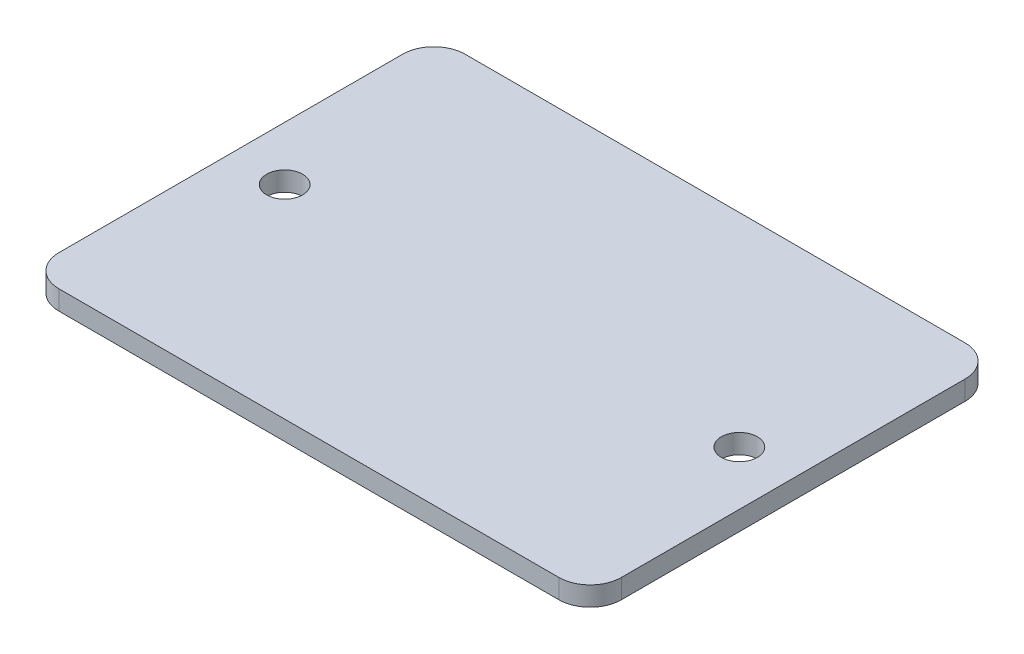
SolidWorks part; units mm, degrees
ref_plane "Front Plane" through (0, 0, 0) normal (0, 0, 1) x (1, 0, 0)
ref_plane "Top Plane" through (0, 0, 0) normal (0, 1, 0) x (1, 0, 0)
ref_plane "Right Plane" through (0, 0, 0) normal (1, 0, 0) x (0, 0, -1)
sketch "Sketch1" plane through (0, 0, 0) normal (0, 1, 0) x (1, 0, 0)
  line L1 (22.86, -16.51) -> (-22.86, -16.51)
  line L2 (22.86, -16.51) -> (22.86, 16.51)
  line L3 (22.86, 16.51) -> (-22.86, 16.51)
  line L4 (-22.86, -16.51) -> (-22.86, 16.51)
  line L5 (22.86, -16.51) -> (-22.86, 16.51) construction
  line L6 (22.86, 16.51) -> (-22.86, -16.51) construction
  point P0 (0, 0)
  dimension "D1" = 45.72
  dimension "D2" = 33.02
extrude "Boss-Extrude1" add sketch "Sketch1" along normal blind 1.5748
fillet "Fillet1" radius 2.54 4 edges at (-22.86, 0.7874, -16.51) (22.86, 0.7874, -16.51) (22.86, 0.7874, 16.51) (-22.86, 0.7874, 16.51)
sketch "Sketch2" plane through (0, 1.5748, 0) normal (0, 1, 0) x (1, 0, 0)
  line L0 (-18.4785, 0) -> (18.4785, 0) construction
  circle A0 centre (-18.4785, 0) radius 1.4605
  circle A1 centre (18.4785, 0) radius 1.4605
  point P4 (0, 0)
  dimension "D1" = 2.921
  dimension "D2" = 39.878
extrude "Cut-Extrude1" cut sketch "Sketch2" against normal through all
